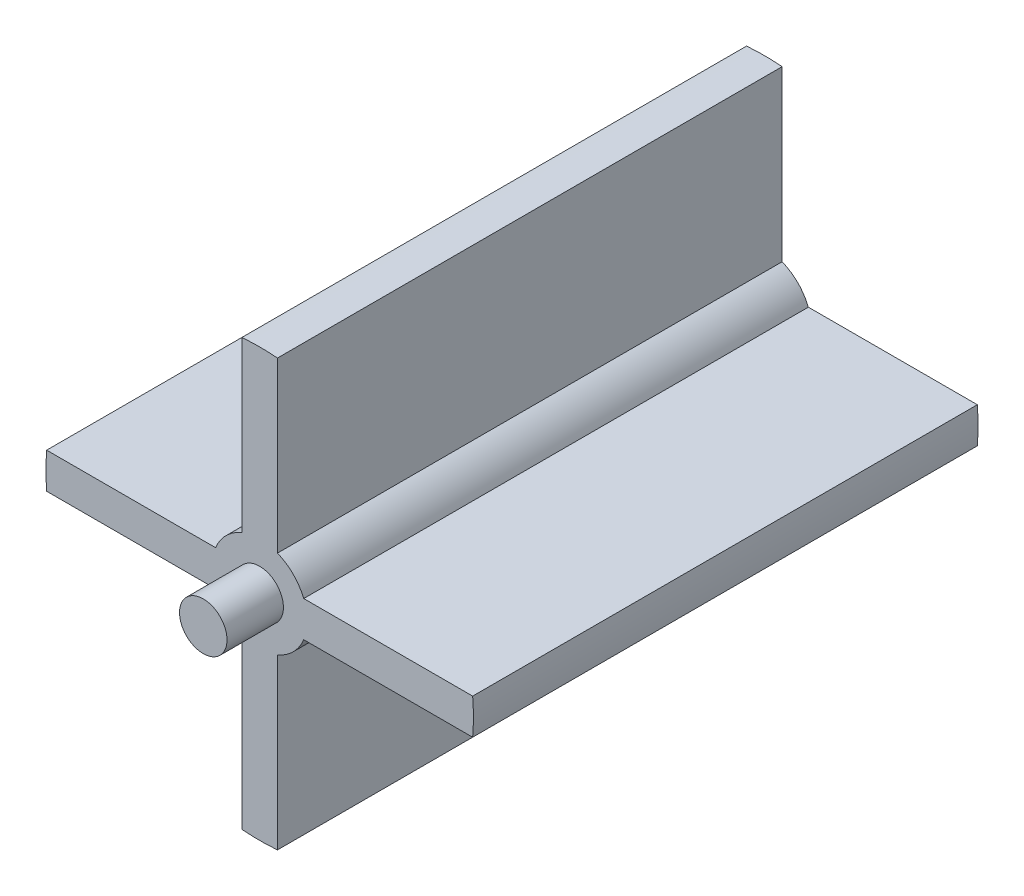
SolidWorks part; units mm, degrees
ref_plane "Front Plane" through (0, 0, 0) normal (0, 0, 1) x (1, 0, 0)
ref_plane "Top Plane" through (0, 0, 0) normal (0, 1, 0) x (1, 0, 0)
ref_plane "Right Plane" through (0, 0, 0) normal (1, 0, 0) x (0, 0, -1)
sketch "Sketch1" plane through (0, 0, 0) normal (0, 0, 1) x (1, 0, 0)
  circle A0 centre (0, 0) radius 36
  dimension "D1" = 72
extrude "Boss-Extrude1" add sketch "Sketch1" along normal blind 85
sketch "Sketch2" plane through (0, 0, 85) normal (0, 0, 1) x (1, 0, 0)
  circle A0 centre (0, 0) radius 4
  dimension "D1" = 8
sketch "Sketch3" plane through (0, 0, 0) normal (0, 0, -1) x (-1, 0, 0)
  circle A0 centre (0, 0) radius 4
  dimension "D1" = 8
extrude "Cut-Extrude2" cut sketch "Sketch3" against normal blind 5
sketch "Sketch4" plane through (0, 0, 0) normal (0, 0, -1) x (-1, 0, 0)
  line L0 (0, -36) -> (0, -8) construction
  line L1 (8, 0) -> (36, 0) construction
  line L2 (0, 7.8049) -> (0, 36) construction
  line L3 (-8, 0) -> (-36, 0) construction
  line L4 (-35.8748, 3) -> (-7.4162, 3)
  line L6 (-7.4162, -3) -> (-35.8748, -3)
  line L7 (-3, -7.4162) -> (-3, -35.8748)
  line L9 (3, -35.8748) -> (3, -7.4162)
  line L10 (7.4162, 3) -> (35.8748, 3)
  line L12 (35.8748, -3) -> (7.4162, -3)
  line L13 (3, 35.8748) -> (3, 7.4162)
  line L15 (-3, 7.4162) -> (-3, 35.8748)
  arc A0 (-3, 7.4162) -> (-7.4162, 3) centre (0, 0) ccw
  arc A1 (35.8748, -3) -> (35.8748, 3) centre (0, 0) ccw
  circle A2 centre (0, 0) radius 36 construction
  arc A3 (-7.4162, -3) -> (-3, -7.4162) centre (0, 0) ccw
  arc A4 (7.4162, 3) -> (3, 7.4162) centre (0, 0) ccw
  arc A5 (3, -7.4162) -> (7.4162, -3) centre (0, 0) ccw
  arc A6 (-3, -35.8748) -> (3, -35.8748) centre (0, 0) ccw
  arc A7 (-35.8748, 3) -> (-35.8748, -3) centre (0, 0) ccw
  arc A8 (3, 35.8748) -> (-3, 35.8748) centre (0, 0) ccw
  dimension "D8" = 8
  dimension "D1" = 3
  dimension "D2" = 3
  dimension "D3" = 3
  dimension "D4" = 3
  dimension "D5" = 3
  dimension "D6" = 3
  dimension "D7" = 3
extrude "Cut-Extrude3" cut sketch "Sketch4" against normal through all flip side to cut
sketch "Sketch5" plane through (0, 0, 0) normal (0, 0, 1) x (1, 0, 0)
  circle A0 centre (-9.3234, 9.512) radius 3.975
  circle A1 centre (9.5329, -9.2187) radius 3.975
  dimension "D1" = 7.95
  dimension "7.95" = 7.95
extrude "Boss-Extrude2" add sketch "Sketch5" along normal blind 14.5 separate body
extrude "Boss-Extrude3" add sketch "Sketch2" along normal blind 9.5
